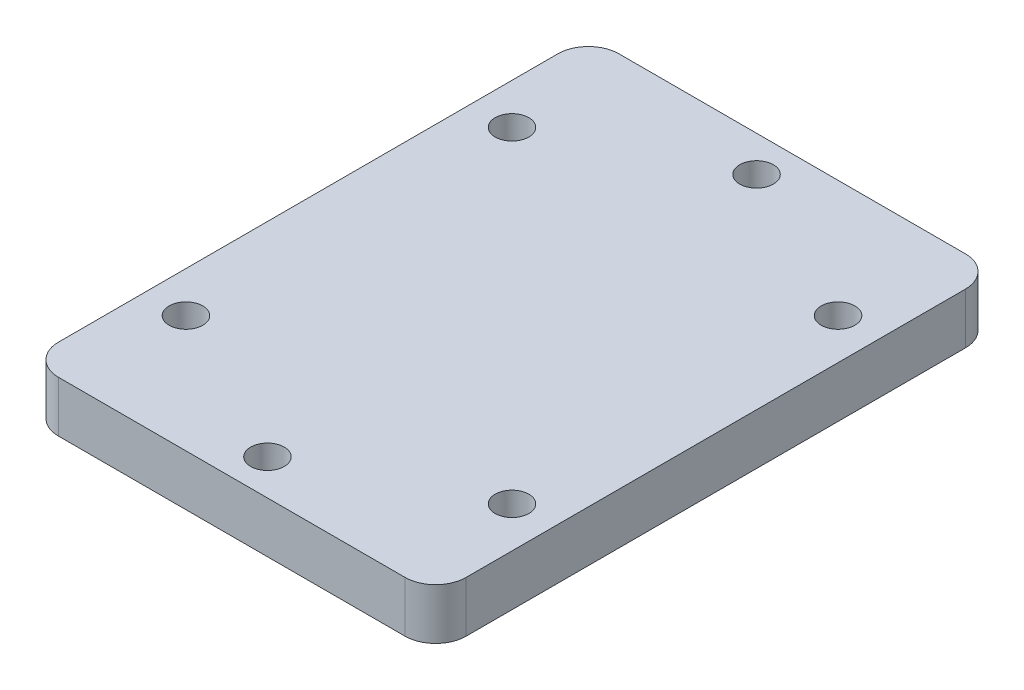
SolidWorks part; units mm, degrees
ref_plane "前视基准面" through (0, 0, 0) normal (0, 0, 1) x (1, 0, 0)
ref_plane "上视基准面" through (0, 0, 0) normal (0, 1, 0) x (1, 0, 0)
ref_plane "右视基准面" through (0, 0, 0) normal (1, 0, 0) x (0, 0, -1)
sketch "草图1" plane through (0, 0, 0) normal (0, 1, 0) x (1, 0, 0)
  line L1 (-20, -27.5) -> (20, -27.5)
  line L2 (-20, -27.5) -> (-20, 27.5)
  line L3 (-20, 27.5) -> (20, 27.5)
  line L4 (20, -27.5) -> (20, 27.5)
  line L5 (-20, -27.5) -> (20, 27.5) construction
  line L6 (-20, 27.5) -> (20, -27.5) construction
  line L7 (-16, -16) -> (16, -16) construction
  line L8 (-16, -16) -> (-16, 16) construction
  line L9 (-16, 16) -> (16, 16) construction
  line L10 (16, -16) -> (16, 16) construction
  line L11 (-16, -16) -> (16, 16) construction
  line L12 (-16, 16) -> (16, -16) construction
  circle A0 centre (-16, 16) radius 1.65
  circle A1 centre (16, 16) radius 1.65
  circle A2 centre (16, -16) radius 1.65
  circle A3 centre (-16, -16) radius 1.65
  point P0 (0, 0)
  point P6 (0, 0)
  dimension "D3" = 3.3
  dimension "D1" = 40
  dimension "D2" = 55
  dimension "D4" = 32
extrude "凸台-拉伸1" add sketch "草图1" along normal blind 5
sketch "草图2" plane through (0, 0, 0) normal (1, 0, 0) x (0, 0, -1)
  line L0 (0, 0) -> (0, -7.0339) construction
  line L1 (-18.5, 0) -> (-8.5, 0)
  line L2 (-27.5, 0) -> (27.5, 0) construction
  line L3 (-8.5, 0) -> (-11, -2.5)
  line L4 (-11, -2.5) -> (-16, -2.5)
  line L5 (-16, -2.5) -> (-18.5, 0)
  line L6 (11, -2.5) -> (16, -2.5)
  line L7 (8.5, 0) -> (11, -2.5)
  line L8 (18.5, 0) -> (8.5, 0)
  line L9 (16, -2.5) -> (18.5, 0)
  point P13 (-11.9155, 0)
  point P14 (-9.2218, 0)
  dimension "D1" = 5
  dimension "D2" = 135
  dimension "D3" = 2.5
  dimension "D4" = 11
extrude "凸台-拉伸2" add sketch "草图2" along normal mid plane 6
sketch "草图3" plane through (0, 5, 0) normal (0, 1, 0) x (1, 0, 0)
  line L0 (0, -24) -> (0, 24) construction
  line L1 (20, 27.5) -> (-20, 27.5) construction
  circle A0 centre (0, -24) radius 1.65
  circle A1 centre (0, 24) radius 1.65
  point P5 (0, 0)
  dimension "D1" = 3.3
  dimension "D2" = 3.5
extrude "切除-拉伸1" cut sketch "草图3" against normal through all
sketch "草图4" plane through (0, 0, 0) normal (0, -1, 0) x (1, 0, 0)
  line L1 (-14.3834, 18.8) -> (-17.6166, 18.8)
  line L2 (-17.6166, 18.8) -> (-19.2332, 16)
  line L3 (-19.2332, 16) -> (-17.6166, 13.2)
  line L4 (-17.6166, 13.2) -> (-14.3834, 13.2)
  line L5 (-14.3834, 13.2) -> (-12.7668, 16)
  line L6 (-12.7668, 16) -> (-14.3834, 18.8)
  line L7 (17.6166, 18.8) -> (14.3834, 18.8)
  line L8 (14.3834, 18.8) -> (12.7668, 16)
  line L9 (12.7668, 16) -> (14.3834, 13.2)
  line L10 (14.3834, 13.2) -> (17.6166, 13.2)
  line L11 (17.6166, 13.2) -> (19.2332, 16)
  line L12 (19.2332, 16) -> (17.6166, 18.8)
  line L13 (14.3834, -13.2) -> (12.7668, -16)
  line L14 (12.7668, -16) -> (14.3834, -18.8)
  line L15 (14.3834, -18.8) -> (17.6166, -18.8)
  line L16 (17.6166, -18.8) -> (19.2332, -16)
  line L17 (19.2332, -16) -> (17.6166, -13.2)
  line L18 (17.6166, -13.2) -> (14.3834, -13.2)
  line L19 (-17.6166, -13.2) -> (-19.2332, -16)
  line L20 (-19.2332, -16) -> (-17.6166, -18.8)
  line L21 (-17.6166, -18.8) -> (-14.3834, -18.8)
  line L22 (-14.3834, -18.8) -> (-12.7668, -16)
  line L23 (-12.7668, -16) -> (-14.3834, -13.2)
  line L24 (-14.3834, -13.2) -> (-17.6166, -13.2)
  circle A0 centre (-16, 16) radius 2.8 construction
  circle A1 centre (16, 16) radius 2.8 construction
  circle A2 centre (16, -16) radius 2.8 construction
  circle A3 centre (-16, -16) radius 2.8 construction
  dimension "D1" = 5.6
extrude "切除-拉伸2" cut sketch "草图4" against normal offset from surface (2.5 mm away) 2.5 up to face at (0, 5, -22.35)
fillet "圆角1" radius 3 4 edges at (-20, 2.5, 27.5) (20, 2.5, -27.5) (-20, 2.5, -27.5) (20, 2.5, 27.5)
